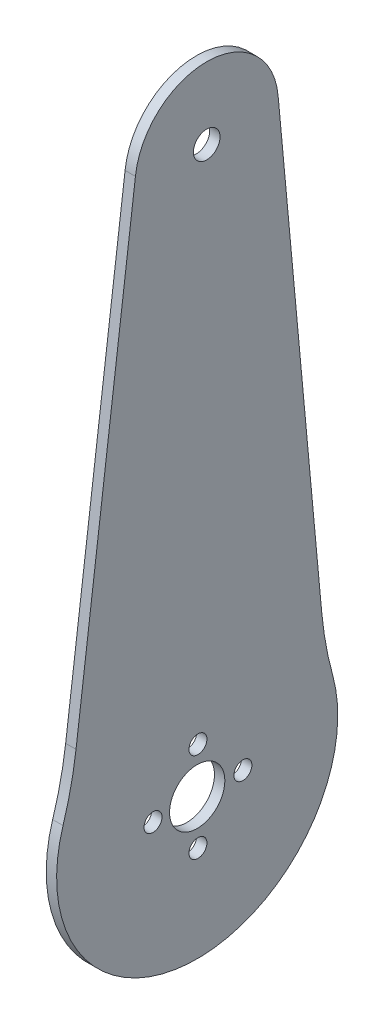
SolidWorks part; units mm, degrees
ref_plane "前基準面" through (0, 0, 0) normal (0, 0, 1) x (1, 0, 0)
ref_plane "上基準面" through (0, 0, 0) normal (0, 1, 0) x (1, 0, 0)
ref_plane "右基準面" through (0, 0, 0) normal (1, 0, 0) x (0, 0, -1)
sketch "草圖2" plane through (0, 0, 0) normal (1, 0, 0) x (0, 0, -1)
  line L0 (11.7185, 46.2767) -> (18.0121, -21.4416)
  line L1 (-8.93, 46.628) -> (-17.523, -20.8372)
  circle A0 centre (0, -35.5155) radius 4
  circle A1 centre (-6.3885, -35.5155) radius 1.3
  circle A2 centre (0.1115, -29.0155) radius 1.3
  circle A3 centre (6.6115, -35.5155) radius 1.3
  circle A4 centre (0.1115, -42.0155) radius 1.3
  circle A7 centre (1.3776, 45.4728) radius 1.925
  arc A8 (-20.0208, -31.9867) -> (20.1292, -32.6696) centre (0, -35.5155) ccw
  arc A9 (-19.4024, -29.4465) -> (19.5975, -30.1099) centre (0, -35.5155) ccw
  arc A10 (11.7185, 46.2767) -> (-8.93, 46.628) centre (1.3776, 45.4728) ccw
  arc A11 (18.0121, -21.4416) -> (19.5975, -30.1099) centre (67.7975, -16.8147) ccw
  arc A12 (-19.4024, -29.4465) -> (-17.523, -20.8372) centre (-67.1223, -14.5197) ccw
extrude "填料-伸長1" add sketch "草圖2" along normal blind 1.5
